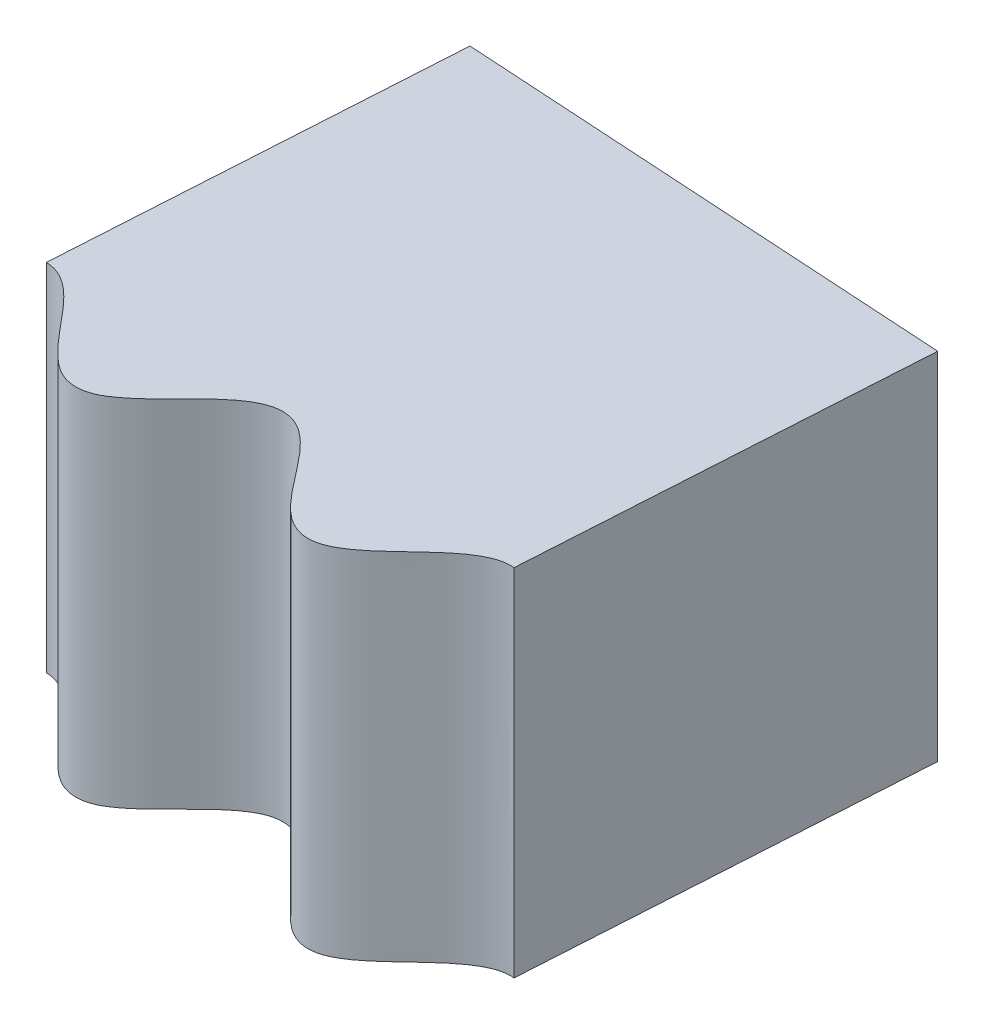
SolidWorks part; units mm, degrees
ref_plane "Front Plane" through (0, 0, 0) normal (0, 0, 1) x (1, 0, 0)
ref_plane "Top Plane" through (0, 0, 0) normal (0, 1, 0) x (1, 0, 0)
ref_plane "Right Plane" through (0, 0, 0) normal (1, 0, 0) x (0, 0, -1)
sketch "Sketch1" plane through (0, 0, 0) normal (0, 1, 0) x (1, 0, 0)
  line L0 (0, 80) -> (0, 85)
  line L1 (80, 0) -> (85, 0)
  arc A0 (0, 85) -> (85, 0) centre (0, 0) cw
  spline S0 degree 4 number of poles 787 (78.6783, -11.6044) -> (-11.7407, 79.6091) construction
  spline S1 degree 4 number of poles 651 (80, 0) -> (0, 80)
  dimension "D1" = 85
extrude "Boss-Extrude1" add sketch "Sketch1" along normal blind 4
sketch "Sketch3" plane through (0, 4, 0) normal (0, 1, 0) x (1, 0, 0)
  line L0 (2.1072, 80.4718) -> (2.3821, 84.9666)
  line L3 (0, 85) -> (0, 80) construction
  line L4 (0, 85) -> (0, 80)
  arc A1 (85, 0) -> (0, 85) centre (0, 0) ccw construction
  arc A3 (2.3821, 84.9666) -> (0, 85) centre (0, 0) ccw
  spline S0 degree 4 number of poles 651 (0, 80) -> (80, 0) construction
  dimension "D1" = 3.5
  dimension "D2" = 1.5
extrude "Cut-Extrude2" cut sketch "Sketch3" against normal through all both and the other way through all
sketch "Sketch2" plane through (0, 4, 0) normal (0, 1, 0) x (1, 0, 0)
  line L0 (7.9904, 84.6236) -> (7.7155, 80.1286)
  line L1 (2.3821, 84.9666) -> (2.1072, 80.4718) construction
  arc A0 (85, 0) -> (2.3821, 84.9666) centre (0, 0) ccw construction
  arc A1 (85, 0) -> (7.9904, 84.6236) centre (0, 0) ccw
  spline S1 degree 4 number of poles 642 (2.1072, 80.4718) -> (80, 0) construction
  dimension "D1" = 4
extrude "Cut-Extrude1" cut sketch "Sketch2" against normal through all both and the other way through all
sketch "Sketch4" plane through (0, 4, 0) normal (0, 1, 0) x (1, 0, 0)
  line L0 (2.3821, 84.9666) -> (7.9904, 84.6236)
  arc A0 (7.9904, 84.6236) -> (2.3821, 84.9666) centre (0, 0) ccw construction
  arc A1 (7.9904, 84.6236) -> (2.3821, 84.9666) centre (0, 0) ccw
extrude "Cut-Extrude3" cut sketch "Sketch4" against normal through all both and the other way through all
ref_plane "Plane1" through (0, 0, 0) normal (0.9981, 0, 0.061) x (0.061, 0, -0.9981)
